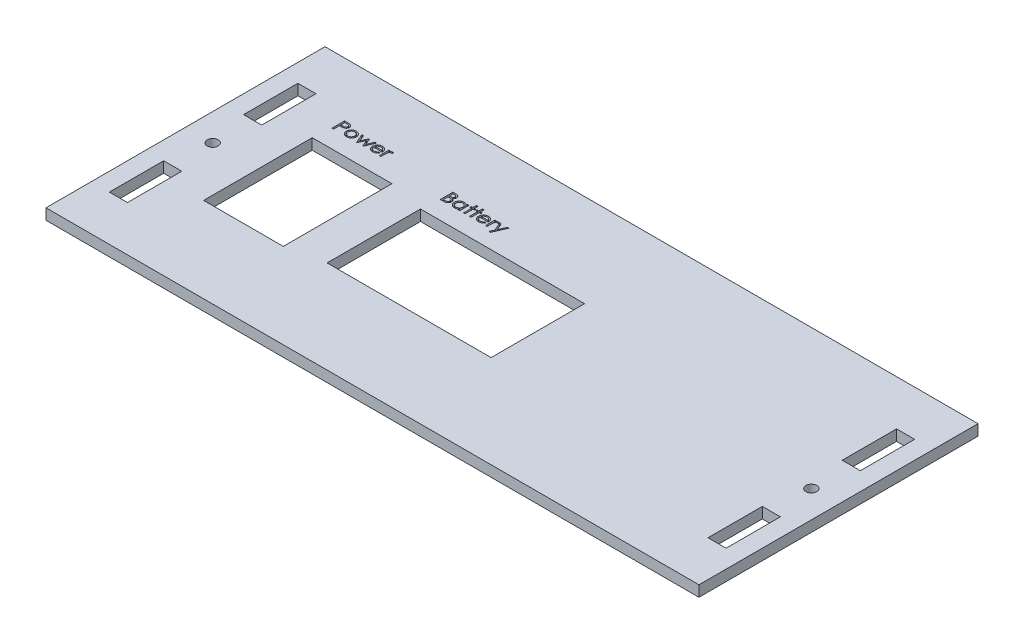
SolidWorks part; units mm, degrees
material "PMMA"
ref_plane "Front Plane" through (0, 0, 0) normal (0, 0, 1) x (1, 0, 0)
ref_plane "Top Plane" through (0, 0, 0) normal (0, 1, 0) x (1, 0, 0)
ref_plane "Right Plane" through (0, 0, 0) normal (1, 0, 0) x (0, 0, -1)
sketch "Schizzo1" plane through (0, 0, 0) normal (0, 1, 0) x (1, 0, 0)
  line L0 (-90.17, -38.535) -> (90.17, 38.535) construction
  line L1 (-90.17, 38.535) -> (90.17, 38.535)
  line L2 (-90.17, 38.535) -> (-90.17, -38.535)
  line L3 (-90.17, -38.535) -> (90.17, -38.535)
  line L4 (90.17, 38.535) -> (90.17, -38.535)
  point P4 (0, 0)
  dimension "D1" = 77.07
  dimension "D2" = 180.34
extrude "Estrusione-Estrusione1" add sketch "Schizzo1" along normal blind 3
sketch "Schizzo2" plane through (0, 0, 0) normal (0, 1, 0) x (1, 0, 0)
  line L0 (-90.17, 38.535) -> (-90.17, -38.535) construction
  line L1 (-85.17, 26.035) -> (-80.17, 26.035)
  line L2 (-85.17, 26.035) -> (-85.17, 11.035)
  line L3 (-85.17, 11.035) -> (-80.17, 11.035)
  line L4 (-80.17, 26.035) -> (-80.17, 11.035)
  line L5 (90.17, 38.535) -> (-90.17, 38.535) construction
  line L6 (-90.17, 0) -> (90.17, 0) construction
  line L7 (90.17, -38.535) -> (90.17, 38.535) construction
  line L8 (0, 38.535) -> (0, -38.535) construction
  line L9 (-90.17, -38.535) -> (90.17, -38.535) construction
  line L10 (-85.17, -26.035) -> (-85.17, -11.035)
  line L11 (-85.17, -26.035) -> (-80.17, -26.035)
  line L12 (-80.17, -26.035) -> (-80.17, -11.035)
  line L13 (-85.17, -11.035) -> (-80.17, -11.035)
  line L14 (85.17, -26.035) -> (85.17, -11.035)
  line L15 (85.17, -11.035) -> (80.17, -11.035)
  line L16 (80.17, -26.035) -> (80.17, -11.035)
  line L17 (85.17, -26.035) -> (80.17, -26.035)
  line L18 (85.17, 26.035) -> (85.17, 11.035)
  line L19 (85.17, 26.035) -> (80.17, 26.035)
  line L20 (80.17, 26.035) -> (80.17, 11.035)
  line L21 (85.17, 11.035) -> (80.17, 11.035)
  line L22 (-82.67, 11.035) -> (-82.67, -11.035) construction
  circle A0 centre (-82.67, 0) radius 1.5
  circle A1 centre (82.67, 0) radius 1.5
  dimension "D5" = 3
  dimension "D2" = 5
  dimension "D1" = 15
  dimension "D3" = 5
  dimension "D4" = 12.5
extrude "Taglio-Estrusione1" cut sketch "Schizzo2" along direction (0, 1, 0) on the side of the normal through all
sketch "Schizzo3" plane through (0, 0, 0) normal (0, 1, 0) x (1, 0, 0)
  line L0 (-90.17, 0) -> (90.17, 0) construction
  line L1 (-38.17, 12.9) -> (7.13, 12.9)
  line L2 (-38.17, 12.9) -> (-38.17, -12.9)
  line L3 (-38.17, -12.9) -> (7.13, -12.9)
  line L4 (7.13, 12.9) -> (7.13, -12.9)
  line L5 (-90.17, 38.535) -> (-90.17, -38.535) construction
  line L6 (90.17, -38.535) -> (90.17, 38.535) construction
  line L8 (-70.17, 15) -> (-48.17, 15)
  line L9 (-70.17, 15) -> (-70.17, -15)
  line L10 (-70.17, -15) -> (-48.17, -15)
  line L11 (-48.17, 15) -> (-48.17, -15)
  point P4 (-38.17, 0)
  point P15 (-48.17, 0)
  dimension "D1" = 45.3
  dimension "D2" = 25.8
  dimension "D3" = 10
  dimension "D4" = 22
  dimension "D5" = 30
  dimension "D6" = 20
extrude "Taglio-Estrusione2" cut sketch "Schizzo3" along direction (0, 1, 0) on the side of the normal through all
sketch "Schizzo4" plane through (0, 3, 0) normal (0, 1, 0) x (1, 0, 0)
  line L0 (-38.17, 12.9) -> (-38.17, -12.9) construction
  line L1 (7.13, 12.9) -> (-38.17, 12.9) construction
  text T0 "<b>Battery</b>"
  dimension "D1" = 5
extrude "Taglio-Estrusione3" cut sketch "Schizzo4" along direction (0, 1, 0) on the side against the normal blind 1
sketch "Schizzo5" plane through (0, 3, 0) normal (0, 1, 0) x (1, 0, 0)
  line L0 (-48.17, 15) -> (-70.17, 15) construction
  line L1 (-70.17, 15) -> (-70.17, 20) construction
  text T0 "<b>Power</b>"
  dimension "D1" = 5
extrude "Taglio-Estrusione4" cut sketch "Schizzo5" against normal blind 1
equation "\"Thickness5\"= 5"
equation "\"D1@Estrusione-Estrusione1\"=\"Thickness3\""
equation "\"D2@Schizzo2\"= \"Thickness5\""
equation "\"D3@Schizzo2\"=\"Thickness5\""
equation "\"Thickness3\"= 3"
